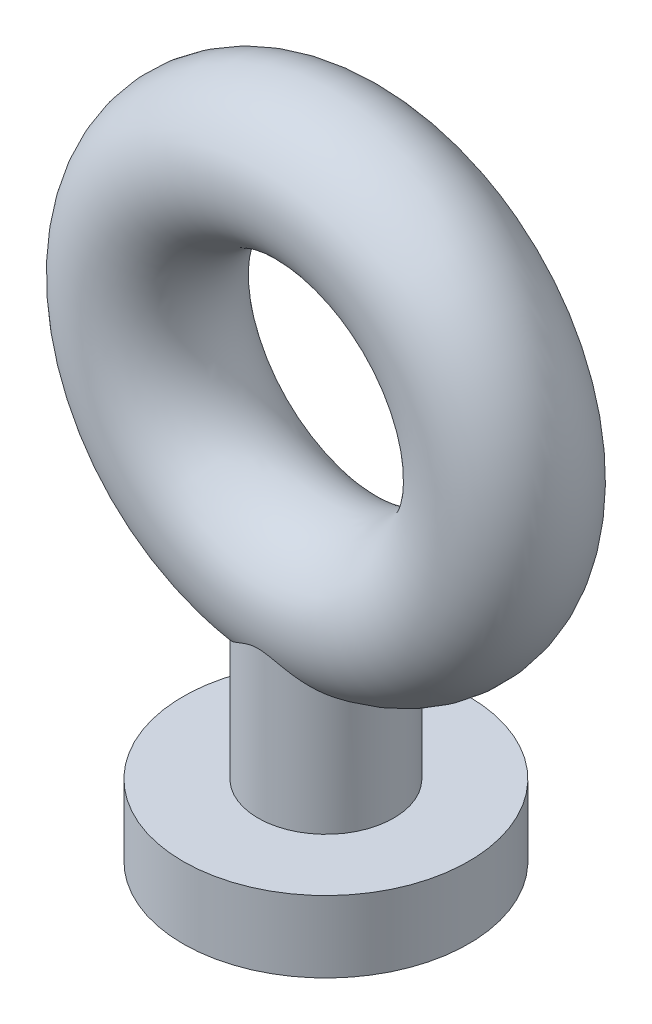
SolidWorks part; units mm, degrees
ref_plane "前视基准面" through (0, 0, 0) normal (0, 0, 1) x (1, 0, 0)
ref_plane "上视基准面" through (0, 0, 0) normal (0, 1, 0) x (1, 0, 0)
ref_plane "右视基准面" through (0, 0, 0) normal (1, 0, 0) x (0, 0, -1)
other "Configuration Table"
sketch "草图1" plane through (0, 0, 0) normal (0, 1, 0) x (1, 0, 0)
  line L0 (0, 0) -> (2.5, 0) construction
  line L1 (0, 0) -> (0, -0.6251) construction
  circle A0 centre (2.5, 0) radius 1
  dimension "D2" = 2
  dimension "D1" = 2.5
revolve "旋转1" add sketch "草图1" angle 360 about L1
sketch "草图2" plane through (0, 0, 0) normal (0, 0, 1) x (1, 0, 0)
  line L0 (0, 0) -> (0, -0.2915) construction
  line L1 (0, -2.5686) -> (0.95, -2.5686)
  line L2 (0.95, -2.5686) -> (0.95, -4.8686)
  line L3 (0.95, -4.8686) -> (2, -4.8686)
  line L4 (2, -4.8686) -> (2, -5.8686)
  line L5 (2, -5.8686) -> (0, -5.8686)
  line L6 (0, -5.8686) -> (0, -2.5686)
  circle A0 centre (0, 0) radius 3.5 construction
  point P10 (0.95, -3.3686)
  dimension "D5" = 1.5
  dimension "D1" = 0.95
  dimension "D2" = 1
  dimension "D3" = 2.3
  dimension "D4" = 2
revolve "旋转2" add sketch "草图2" angle 360 about L0
